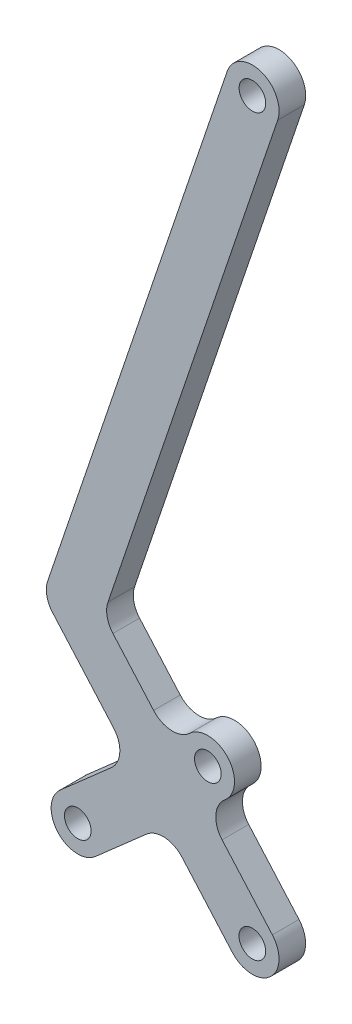
SolidWorks part; units mm, degrees
material "7075-T6, Plate (SS)"
ref_plane "Front Plane" through (0, 0, 0) normal (0, 0, 1) x (1, 0, 0)
ref_plane "Top Plane" through (0, 0, 0) normal (0, 1, 0) x (1, 0, 0)
ref_plane "Right Plane" through (0, 0, 0) normal (1, 0, 0) x (0, 0, -1)
sketch "Sketch1" plane through (0, 0, 0) normal (0, 0, 1) x (1, 0, 0)
  line L1 (-12.0316, 4.0656) -> (-97.6126, -249.1981)
  line L2 (9.4944, -341.6131) -> (-14.4776, -314.3545)
  line L3 (-68.8547, -243.4364) -> (12.0316, -4.0656)
  line L4 (-95.2552, -260.9642) -> (-66.1742, -294.0324)
  line L5 (-71.0726, -250) -> (-95.1359, -241.8687) construction
  line L6 (-71.0726, -250) -> (-90.1462, -266.7738) construction
  line L7 (-30.1649, -278.3452) -> (-29.6393, -277.8829)
  line L8 (-13.3911, -297.4187) -> (-12.8655, -296.9564)
  line L9 (-22.4022, -305.3433) -> (-41.4758, -322.1171) construction
  line L10 (-47.1007, -277.2587) -> (-66.4973, -255.2026)
  line L11 (-67.2607, -310.9682) -> (-91.6283, -332.3977)
  line L12 (-50.4869, -330.0417) -> (-74.8545, -351.4712)
  line L13 (-33.5512, -331.1282) -> (-9.5792, -358.3869)
  line L14 (-39.176, -286.2698) -> (-58.2496, -303.0436) construction
  arc A0 (12.0316, -4.0656) -> (-12.0316, 4.0656) centre (0, 0) ccw
  arc A1 (-9.5792, -358.3869) -> (9.4944, -341.6131) centre (-0.0424, -350) ccw
  arc A2 (-29.6393, -277.8829) -> (-12.8655, -296.9564) centre (-21.2524, -287.4197) cw
  arc A3 (-91.6283, -332.3977) -> (-74.8545, -351.4712) centre (-83.2414, -341.9345) ccw
  arc A4 (-67.2607, -310.9682) -> (-66.1742, -294.0324) centre (-75.1853, -301.9571) ccw
  arc A5 (-33.5512, -331.1282) -> (-50.4869, -330.0417) centre (-42.5623, -339.0529) ccw
  arc A6 (-14.4776, -314.3545) -> (-13.3911, -297.4187) centre (-5.4665, -306.4298) cw
  arc A7 (-30.1649, -278.3452) -> (-47.1007, -277.2587) centre (-38.0895, -269.334) cw
  arc A8 (-97.6126, -249.1981) -> (-95.2552, -260.9642) centre (-86.2441, -253.0396) ccw
  arc A9 (-66.4973, -255.2026) -> (-68.8547, -243.4364) centre (-57.4862, -247.278) cw
  circle A10 centre (-21.2524, -287.4197) radius 6.35
  circle A11 centre (-83.2414, -341.9345) radius 6.35
  circle A12 centre (-0.0424, -350) radius 6.35
  circle A13 centre (0, 0) radius 6.35
  dimension "D9" = 12.7
  dimension "D10" = 12
  dimension "D11" = 12.7
  dimension "D12" = 44.45
  dimension "D1" = 350
  dimension "D2" = 25.4
  dimension "D3" = 250
  dimension "D4" = 120
  dimension "D5" = 25.4
  dimension "D6" = 12.7
  dimension "D7" = 122
  dimension "D8" = 48.3
  dimension "D13" = 0
  dimension "D14" = 0
extrude "Boss-Extrude2" add sketch "Sketch1" along normal blind 12.7
